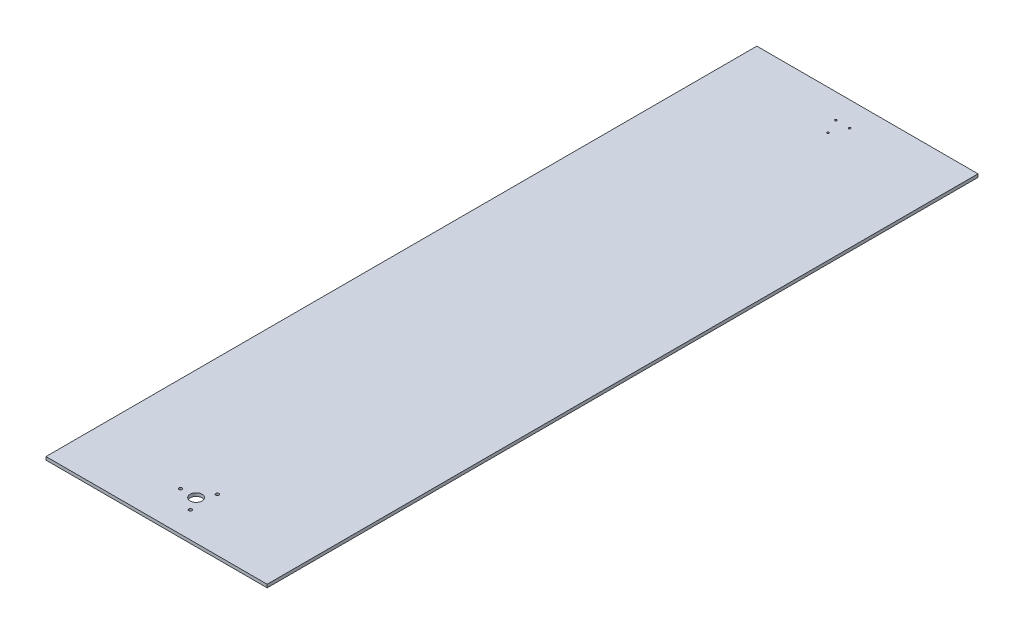
SolidWorks part; units mm, degrees
ref_plane "Front" through (0, 0, 0) normal (0, 0, 1) x (1, 0, 0)
ref_plane "Top" through (0, 0, 0) normal (0, 1, 0) x (1, 0, 0)
ref_plane "Right" through (0, 0, 0) normal (1, 0, 0) x (0, 0, -1)
sketch "Sketch1" plane through (0, 0, 0) normal (0, 1, 0) x (1, 0, 0)
  line L1 (177.8, -63.5) -> (-177.8, -63.5)
  line L2 (177.8, -63.5) -> (177.8, 63.5)
  line L3 (177.8, 63.5) -> (-177.8, 63.5)
  line L4 (-177.8, -63.5) -> (-177.8, 63.5)
  line L5 (177.8, -63.5) -> (-177.8, 63.5) construction
  line L6 (177.8, 63.5) -> (-177.8, -63.5) construction
  circle A0 centre (0, 0) radius 9.525
  circle A1 centre (12.5, 21.6506) radius 2.5527
  circle A2 centre (12.5, -21.6506) radius 2.5527
  circle A3 centre (-25, 0) radius 2.5527
  point P0 (0, 0)
  point P8 (12.5, 21.6506)
  point P17 (0, 0)
  dimension "D1" = 19.05
  dimension "D3" = 5.1054
  dimension "D2" = 25
  dimension "D4" = 355.6
  dimension "D5" = 127
  dimension "D6" = 3
extrude "Boss-Extrude1" add sketch "Sketch1" along normal blind 5.08
sketch "Sketch2" plane through (0, 5.08, 0) normal (0, 1, 0) x (1, 0, 0)
  line L0 (-177.8, 63.5) -> (177.8, 63.5)
  line L1 (-177.8, 63.5) -> (-177.8, 1079.5)
  line L2 (177.8, 63.5) -> (177.8, 1079.5)
  line L3 (-177.8, 1079.5) -> (177.8, 1079.5)
  dimension "D1" = 1016
extrude "Boss-Extrude2" add sketch "Sketch2" against normal up to surface (5.08 mm away) up to face at (0, 0, 0)
sketch "Sketch4" plane through (0, 5.08, 0) normal (0, 1, 0) x (1, 0, 0)
  line L0 (11.1125, 1039.8125) -> (-11.1125, 1039.8125) construction
  line L2 (11.1125, 1039.8125) -> (0, 1016) construction
  line L3 (0, 1016) -> (-11.1125, 1039.8125) construction
  circle A0 centre (11.1125, 1039.8125) radius 1.5875
  circle A1 centre (-11.1125, 1039.8125) radius 1.5875
  circle A2 centre (0, 1016) radius 1.5875
  dimension "D1" = 22.225
  dimension "D2" = 3.175
  dimension "D3" = 1016
  dimension "D4" = 23.8125
extrude "Cut-Extrude1" cut sketch "Sketch4" against normal through all contours A1 | A0 | A2
